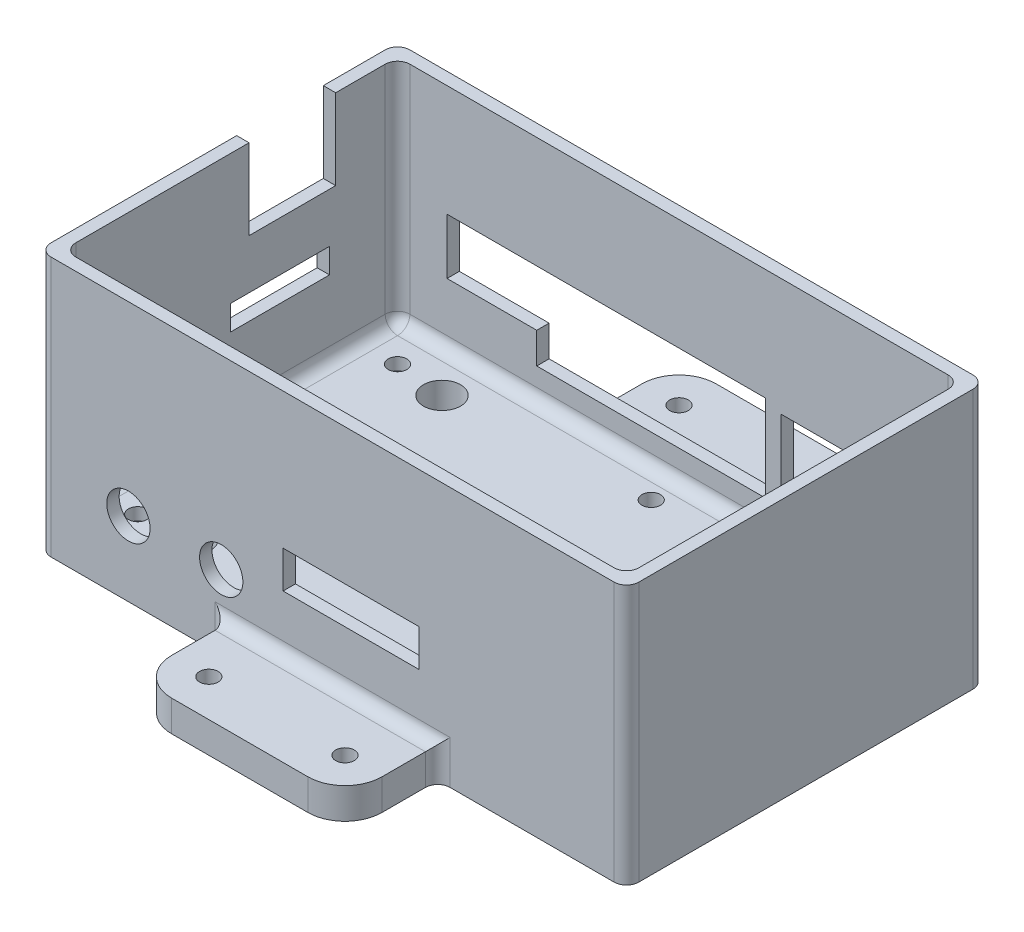
SolidWorks part; units mm, degrees
ref_plane "Front Plane" through (0, 0, 0) normal (0, 0, 1) x (1, 0, 0)
ref_plane "Top Plane" through (0, 0, 0) normal (0, 1, 0) x (1, 0, 0)
ref_plane "Right Plane" through (0, 0, 0) normal (1, 0, 0) x (0, 0, -1)
ref_plane "Plane1" through (0, 0, 0) normal (0, -1, 0) x (1, 0, 0)
sketch "Sketch1" plane through (0, 0, 0) normal (0, -1, 0) x (1, 0, 0)
  line L0 (45.5, -29) -> (45.5, 29)
  line L1 (45.5, 29) -> (-47.5, 29)
  line L2 (-47.5, 29) -> (-47.5, -29)
  line L3 (-47.5, -29) -> (45.5, -29)
extrude "Boss-Extrude1" add sketch "Sketch1" against normal blind 42
sketch "Sketch2" plane through (0, 42, 0) normal (0, 1, 0) x (-1, 0, 0)
  line L0 (-45.5, 27) -> (-45.5, -27)
  line L1 (-45.5, -27) -> (45.5, -27)
  line L2 (45.5, -27) -> (45.5, 27)
  line L3 (45.5, 27) -> (-45.5, 27)
extrude "Cut-Extrude1" cut sketch "Sketch2" against normal blind 19
sketch "Sketch3" plane through (0, 23, 0) normal (0, 1, 0) x (-1, 0, 0)
  line L0 (-35.5, -29) -> (-16.5, -29)
  line L1 (-16.5, -29) -> (-16.5, -27)
  line L2 (-16.5, -27) -> (45.5, -27)
  line L3 (45.5, -27) -> (45.5, 27)
  line L4 (45.5, 27) -> (-45.5, 27)
  line L5 (-45.5, 27) -> (-45.5, -27)
  line L6 (-45.5, -27) -> (-35.5, -27)
  line L7 (-35.5, -27) -> (-35.5, -29)
extrude "Cut-Extrude2" cut sketch "Sketch3" against normal blind 18
sketch "Sketch4" plane through (45.5, 0, 0) normal (1, 0, 0) x (0, 0, -1)
  line L0 (-29, 42) -> (29, 42)
  line L1 (29, 42) -> (29, 0)
  line L2 (29, 0) -> (-29, 0)
  line L3 (-29, 0) -> (-29, 42)
extrude "Boss-Extrude2" add sketch "Sketch4" along normal blind 2
sketch "Sketch5" plane through (0, 0, -29) normal (0, 0, -1) x (-1, 0, 0)
  line L0 (17, 0) -> (-17, 0)
  line L1 (-17, 0) -> (-17, 5)
  line L2 (-17, 5) -> (17, 5)
  line L3 (17, 5) -> (17, 0)
extrude "Boss-Extrude3" add sketch "Sketch5" along normal blind 15
sketch "Sketch6" plane through (-47.5, 0, 0) normal (-1, 0, 0) x (0, 0, 1)
  line L0 (-3, 42) -> (-17, 42)
  line L1 (-17, 42) -> (-17, 29)
  line L2 (-17, 29) -> (-3, 29)
  line L3 (-3, 29) -> (-3, 42)
extrude "Cut-Extrude3" cut sketch "Sketch6" against normal up to next
sketch "Sketch7" plane through (0, 0, -27) normal (0, 0, 1) x (1, 0, 0)
  line L0 (14, 10) -> (14, 24)
  line L1 (14, 24) -> (-37.5, 24)
  line L2 (-37.5, 24) -> (-37.5, 15)
  line L3 (-37.5, 15) -> (-23, 15)
  line L4 (-23, 15) -> (-23, 10)
  line L5 (-23, 10) -> (14, 10)
extrude "Cut-Extrude4" cut sketch "Sketch7" against normal through all
sketch "Sketch8" plane through (-47.5, 0, 0) normal (-1, 0, 0) x (0, 0, 1)
  line L0 (-16, 17) -> (0, 17)
  line L1 (0, 17) -> (0, 21)
  line L2 (0, 21) -> (-16, 21)
  line L3 (-16, 21) -> (-16, 17)
extrude "Cut-Extrude5" cut sketch "Sketch8" against normal up to next
sketch "Sketch9" plane through (0, 0, 29) normal (0, 0, 1) x (1, 0, 0)
  line L0 (-8, 20) -> (-8, 14)
  line L1 (-8, 14) -> (14, 14)
  line L2 (14, 14) -> (14, 20)
  line L3 (14, 20) -> (-8, 20)
extrude "Cut-Extrude6" cut sketch "Sketch9" against normal through all
sketch "Sketch10" plane through (0, 0, 29) normal (0, 0, 1) x (1, 0, 0)
  line L0 (-17, 5) -> (17, 5)
  line L1 (17, 5) -> (17, 0)
  line L2 (17, 0) -> (-17, 0)
  line L3 (-17, 0) -> (-17, 5)
extrude "Boss-Extrude4" add sketch "Sketch10" along normal blind 15
hole_wizard "Ø3.0 (3) Diameter Hole1" positions "Sketch12" profile "Sketch11" hole size "Ø3.0" standard "ANSI Metric"
sketch "Sketch12" plane through (0, 5, 0) normal (0, 1, 0) x (1, 0, 0)
  point P0 (11, -38)
  point P1 (-11, 38)
  point P2 (-11, -38)
  point P3 (11, 38)
  point P4 (0, 22.5)
  point P5 (0, -22.5)
  point P6 (-39.5, -12.925)
  point P7 (-39.5, -9.425)
sketch "Sketch11" plane through (11, 5, 38) normal (1, 0, 0) x (0, 0, 1)
  line L0 (0, 0) -> (0, 5)
  line L1 (0, 5) -> (1.5, 5)
  line L2 (1.5, 5) -> (1.5, 0)
  line L5 (1.5, 0) -> (0, 0)
  line L11 (0, -6.35) -> (0, 107.95) construction
  dimension "Thru Hole Dia." = 3
  dimension "Thru Hole Depth" = 5
hole_wizard "Ø6.0 (6) Diameter Hole1" positions "Sketch14" profile "Sketch13" hole size "Ø6.0" standard "ANSI Metric"
sketch "Sketch14" plane through (0, 5, 0) normal (0, 1, 0) x (1, 0, 0)
  point P0 (31.5403, -20.2266)
  point P1 (-31.5403, -20.2266)
  point P2 (31.5403, 20.2266)
  point P3 (-31.5403, 20.2266)
sketch "Sketch13" plane through (31.5403, 5, 20.2266) normal (1, 0, 0) x (0, 0, 1)
  line L0 (0, 0) -> (0, 5)
  line L1 (0, 5) -> (3, 5)
  line L2 (3, 5) -> (3, 0)
  line L5 (3, 0) -> (0, 0)
  line L11 (0, -6.35) -> (0, 107.95) construction
  dimension "Thru Hole Dia." = 6
  dimension "Thru Hole Depth" = 5
hole_wizard "Ø7.0 (7) Diameter Hole1" positions "Sketch16" profile "Sketch15" hole size "Ø7.0" standard "ANSI Metric"
sketch "Sketch16" plane through (0, 0, 29) normal (0, 0, 1) x (1, 0, 0)
  point P0 (-18, 12)
  point P1 (-33, 12)
sketch "Sketch15" plane through (-18, 12, 29) normal (1, 0, 0) x (0, -1, 0)
  line L0 (0, 0) -> (0, 2)
  line L1 (0, 2) -> (3.5, 2)
  line L2 (3.5, 2) -> (3.5, 0)
  line L5 (3.5, 0) -> (0, 0)
  line L11 (0, -6.35) -> (0, 107.95) construction
  dimension "Thru Hole Dia." = 7
  dimension "Thru Hole Depth" = 2
hole_wizard "Ø8.0 (8) Diameter Hole1" positions "Sketch18" profile "Sketch17" hole size "Ø8.0" standard "ANSI Metric"
sketch "Sketch18" plane through (-47.5, 0, 0) normal (-1, 0, 0) x (0, 0, 1)
  point P0 (11.228, 17.5)
sketch "Sketch17" plane through (-47.5, 17.5, 11.228) normal (0, 1, 0) x (0, 0, 1)
  line L0 (0, 0) -> (0, 2)
  line L1 (0, 2) -> (4, 2)
  line L2 (4, 2) -> (4, 0)
  line L5 (4, 0) -> (0, 0)
  line L11 (0, -6.35) -> (0, 107.95) construction
  dimension "Thru Hole Dia." = 8
  dimension "Thru Hole Depth" = 2
hole_wizard "CBORE for M2.5 Hex Head Machine Screw1" positions "Sketch20" profile "Sketch19" counterbore size "M2.5" standard "ANSI Metric"
sketch "Sketch20" plane through (0, 0, 0) normal (0, -1, 0) x (-1, 0, 0)
  point P0 (-39.5, -21)
  point P1 (39.5, -21)
  point P2 (-39.5, 21)
  point P3 (39.5, 21)
sketch "Sketch19" plane through (39.5, 0, 21) normal (1, 0, 0) x (0, 0, -1)
  line L0 (0, 0) -> (0, 42)
  line L1 (0, 42) -> (1.5, 42)
  line L3 (1.5, 42) -> (1.5, 3)
  line L4 (1.5, 3) -> (3, 3)
  line L5 (3, 3) -> (3, 0)
  line L7 (3, 0) -> (0, 0)
  line L11 (0, -6.35) -> (0, 107.95) construction
  dimension "Thru Hole Dia." = 3
  dimension "Thru Hole Depth" = 42
  dimension "C'Bore Dia." = 6
  dimension "C'Bore Depth" = 3
fillet "Fillet1" radius 2 19 edges at (40.5, 5, -27) (45.5, 23.5, -27) (-45.5, 23.5, -27) (-14.5, 5, -27) (45.5, 5, 0) (45.5, 23.5, 27) (-45.5, 5, 0) (0, 5, 27) (-45.5, 23.5, 27) (17, 2.5, 29) (0, 5, 29) (-17, 2.5, 29) (47.5, 21, 29) (-0.25, 5, -29) (-17, 2.5, -29) (-47.5, 21, 29) (17, 2.5, -29) (47.5, 21, -29) (-47.5, 21, -29)
fillet "Fillet2" radius 6 4 edges at (17, 2.5, 44) (-17, 2.5, 44) (17, 2.5, -44) (-17, 2.5, -44)
